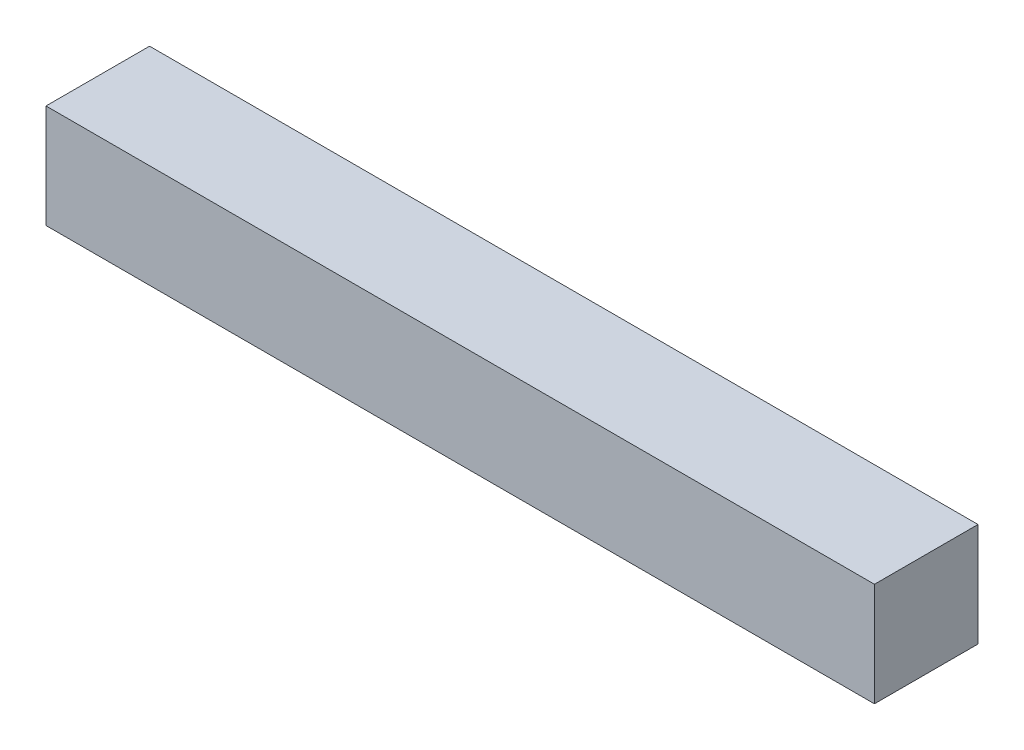
SolidWorks part; units mm, degrees
ref_plane "Front Plane" through (0, 0, 0) normal (0, 0, 1) x (1, 0, 0)
ref_plane "Top Plane" through (0, 0, 0) normal (0, 1, 0) x (1, 0, 0)
ref_plane "Right Plane" through (0, 0, 0) normal (1, 0, 0) x (0, 0, -1)
sketch "Sketch1" plane through (0, 0, 0) normal (0, 1, 0) x (1, 0, 0)
  line L0 (-12.7, 0) -> (12.7, 0) construction
  line L1 (-12.7, 1.5875) -> (12.7, 1.5875)
  line L2 (-12.7, 1.5875) -> (-12.7, -1.5875)
  line L3 (-12.7, -1.5875) -> (12.7, -1.5875)
  line L4 (12.7, 1.5875) -> (12.7, -1.5875)
  dimension "Square Size" = 3.175
  dimension "Length" = 25.4
extrude "Extrude1" add sketch "Sketch1" against normal blind 3.175
sketch "Sketch2" plane through (44.45, 6.35, 1.5875) normal (0, 0, -1) x (-1, 0, 0)
  line L0 (33.3375, -7.9375) -> (55.5625, -7.9375) construction
  line L1 (33.3375, -6.35) -> (55.5625, -6.35)
  line L2 (33.3375, -9.525) -> (55.5625, -9.525)
  line L5 (57.15, -7.9375) -> (55.5625, -7.9375) construction
  line L6 (33.3375, -7.9375) -> (31.75, -7.9375) construction
  line L7 (31.75, -9.525) -> (31.75, -6.35) construction
  line L8 (57.15, -9.525) -> (57.15, -6.35) construction
  line L9 (31.75, -6.35) -> (57.15, -6.35) construction
  arc A0 (33.3375, -6.35) -> (33.3375, -9.525) centre (33.3375, -7.9375) ccw
  arc A1 (55.5625, -9.525) -> (55.5625, -6.35) centre (55.5625, -7.9375) ccw
  point P2 (44.45, -7.9375)
extrude "Extrude2" [suppressed] cut sketch "Sketch2" along normal through all flip side to cut
sketch "Sketch3" plane through (0, 0, 0) normal (0, 1, 0) x (1, 0, 0)
  line L0 (0, -1.5875) -> (0, 1.5875) construction
  line L1 (-12.7, -1.5875) -> (12.7, -1.5875) construction
  line L2 (12.7, 1.5875) -> (-12.7, 1.5875) construction
  dimension "D1" = 3.175
